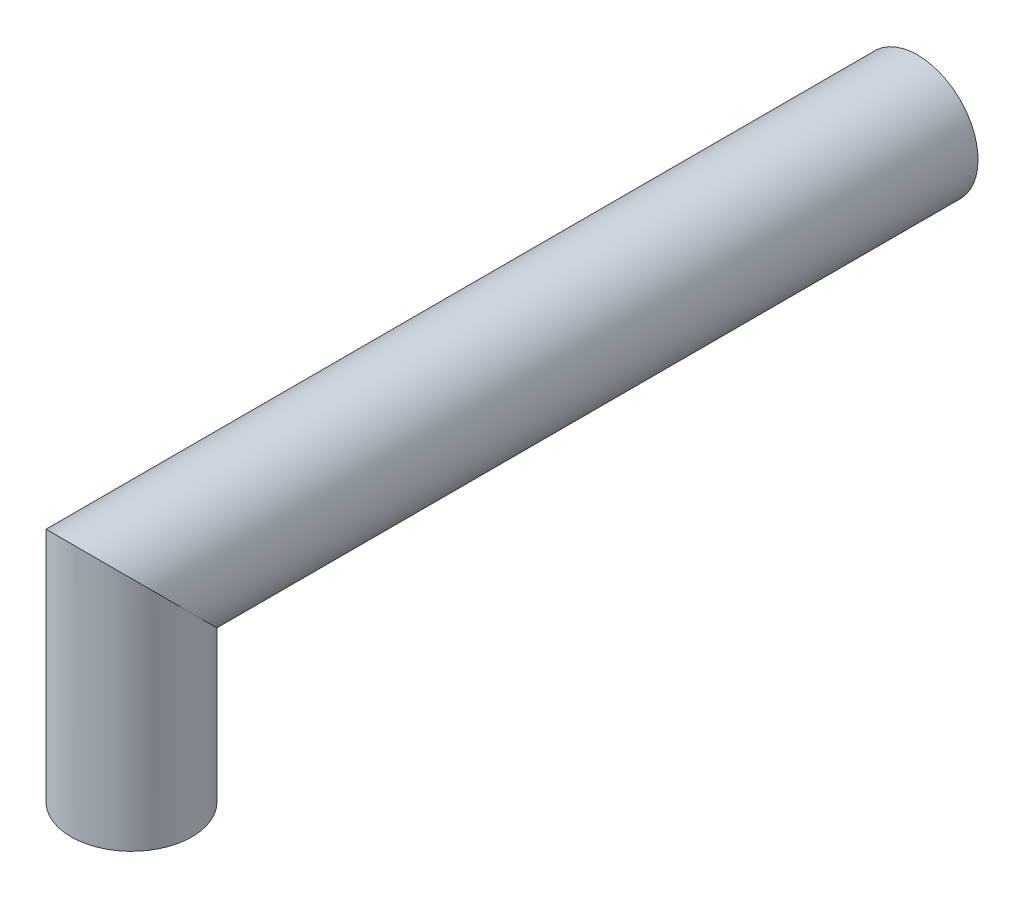
SolidWorks part; units mm, degrees
ref_plane "Front Plane" through (0, 0, 0) normal (0, 0, 1) x (1, 0, 0)
ref_plane "Top Plane" through (0, 0, 0) normal (0, 1, 0) x (1, 0, 0)
ref_plane "Right Plane" through (0, 0, 0) normal (1, 0, 0) x (0, 0, -1)
sketch "Sketch1" plane through (0, 0, 0) normal (0, 1, 0) x (1, 0, 0)
  line L0 (0, -5.5) -> (0, 5.5) construction
  circle A0 centre (0, 0) radius 5
  dimension "D1" = 10
sketch "Sketch2" plane through (0, 0, 0) normal (1, 0, 0) x (0, 0, -1)
  line L0 (0, 0) -> (0, 16)
  line L1 (5, 0) -> (-5, 0) construction
  line L2 (0, 16) -> (65, 16)
sweep "Sweep1" add profiles "Sketch1" path "Sketch2"
